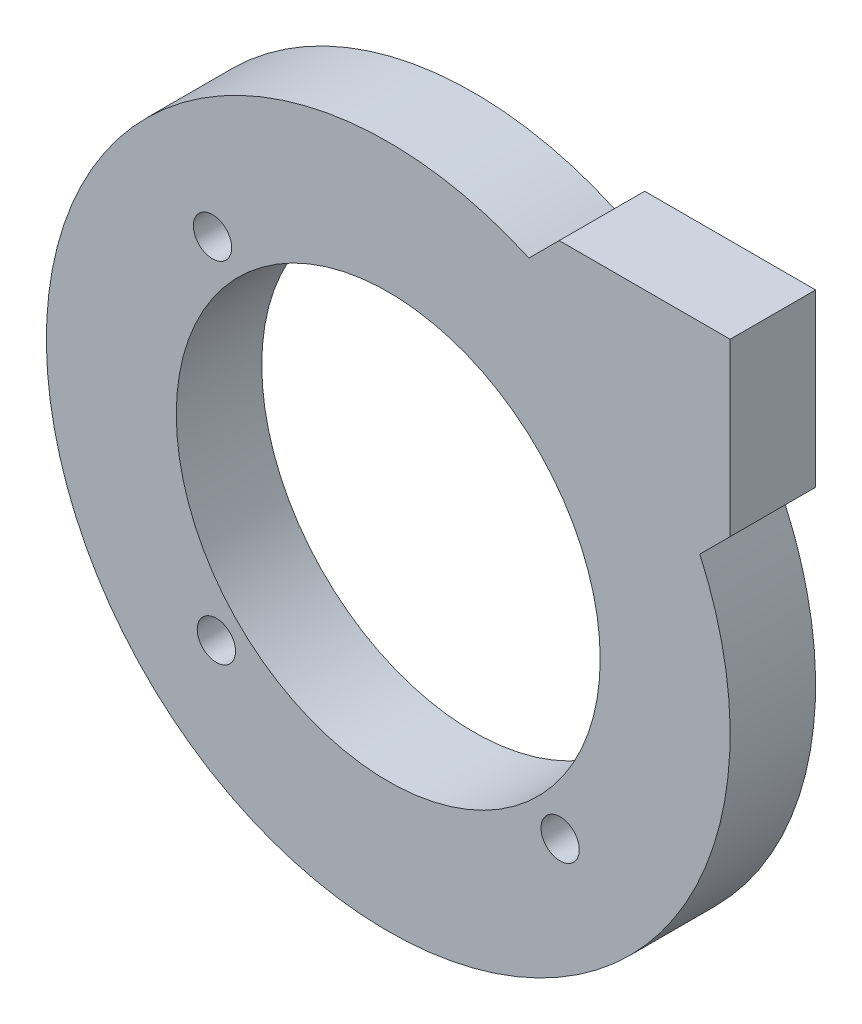
SolidWorks part; units mm, degrees
ref_plane "Front Plane" through (0, 0, 0) normal (0, 0, 1) x (1, 0, 0)
ref_plane "Top Plane" through (0, 0, 0) normal (0, 1, 0) x (1, 0, 0)
ref_plane "Right Plane" through (0, 0, 0) normal (1, 0, 0) x (0, 0, -1)
sketch "Sketch1" plane through (0, 0, 0) normal (0, 0, 1) x (1, 0, 0)
  line L0 (23.1505, 10.4505) -> (25.4, 12.7)
  line L2 (25.4, 0) -> (0, 25.4) construction
  line L3 (12.7, 25.4) -> (25.4, 25.4)
  line L4 (25.4, 25.4) -> (0, 0) construction
  line L6 (25.4, 25.4) -> (25.4, 12.7)
  line L9 (10.4505, 23.1505) -> (12.7, 25.4)
  arc A0 (10.4505, 23.1505) -> (23.1505, 10.4505) centre (0, 0) ccw
  circle A1 centre (0, 0) radius 15.748
extrude "Boss-Extrude1" add sketch "Sketch1" along normal blind 6.35
sketch "Sketch2" plane through (0, 0, 6.35) normal (0, 0, 1) x (1, 0, 0)
  line L0 (25.4, 25.4) -> (11.1355, 11.1355)
  line L1 (11.1355, 11.1355) -> (-17.9605, -17.9605) construction
  line L2 (0, 0) -> (0, -25.4) construction
  circle A0 centre (0, 0) radius 15.748 construction
  circle A4 centre (12.7691, -13.0565) radius 1.4224
  arc A5 (10.4505, 23.1505) -> (23.1505, 10.4505) centre (0, 0) ccw construction
  circle A6 centre (-13.0565, 12.7691) radius 1.4224
  circle A7 centre (-12.7691, -13.0565) radius 1.4224
extrude "Cut-Extrude2" cut sketch "Sketch2" against normal blind 6.35 contours A6 | A7 | A4
